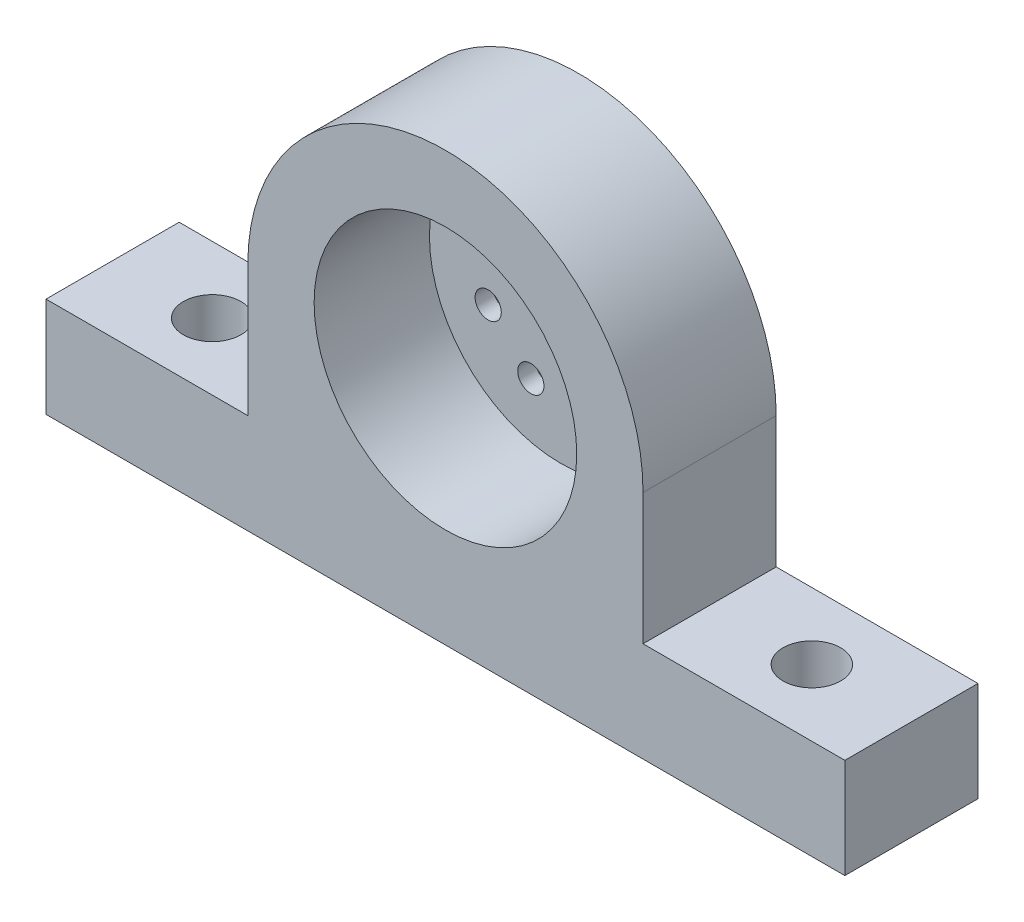
SolidWorks part; units mm, degrees
ref_plane "Front Plane" through (0, 0, 0) normal (0, 0, 1) x (1, 0, 0)
ref_plane "Top Plane" through (0, 0, 0) normal (0, 1, 0) x (1, 0, 0)
ref_plane "Right Plane" through (0, 0, 0) normal (1, 0, 0) x (0, 0, -1)
sketch "Sketch1" plane through (0, 0, 0) normal (0, 0, 1) x (1, 0, 0)
  line L0 (0, 0) -> (0, -56.069) construction
  line L1 (-76.2, -44.05) -> (76.2, -44.05)
  line L2 (-76.2, -44.05) -> (-76.2, -25)
  line L3 (-76.2, -25) -> (76.2, -25)
  line L4 (76.2, -44.05) -> (76.2, -25)
  line L5 (-76.2, -44.05) -> (76.2, -25) construction
  line L6 (-76.2, -25) -> (76.2, -44.05) construction
  line L8 (-37.7, -25) -> (37.7, -25)
  line L9 (-37.7, -25) -> (-37.7, 0)
  line L10 (-37.7, 0) -> (37.7, 0)
  line L11 (37.7, -25) -> (37.7, 0)
  line L12 (-37.7, -25) -> (37.7, 0) construction
  line L13 (-37.7, 0) -> (37.7, -25) construction
  circle A0 centre (0, 0) radius 25
  circle A1 centre (0, 0) radius 20.5
  circle A2 centre (0, 0) radius 12.5
  circle A3 centre (-14.5296, 0.4704) radius 2.5
  circle A4 centre (-10.1362, 11.077) radius 2.5
  circle A5 centre (0.4704, 15.4704) radius 2.5
  circle A6 centre (11.077, 11.077) radius 2.5
  circle A7 centre (15.4704, 0.4704) radius 2.5
  circle A8 centre (11.077, -10.1362) radius 2.5
  circle A9 centre (0, -14.5296) radius 2.5
  circle A10 centre (-10.1362, -10.1362) radius 2.5
  circle A11 centre (0, 0) radius 4
  circle A12 centre (0, 0) radius 10
  arc A13 (-37.7, 0) -> (37.7, 0) centre (0, 0) cw
  point P22 (0, -34.525)
  point P27 (0, -12.5)
  point P34 (-25, 0)
  point P35 (25, 0)
  dimension "D3" = 0
  dimension "D1" = 152.4
  dimension "D2" = 19.05
  dimension "D4" = 0
  dimension "D5" = 12.7
extrude "Boss-Extrude1" add sketch "Sketch1" along normal blind 25.4 contours L1 L4 L3 L8 L2 | A0 L10 L9 L3 | A13 L10 A0 | A1 L10 A0 | A1 L10 A0 | A10 A2 A3 L10 A1 A7 A9 A8 | A7 L10 A1 A3 A2 A6 A5 A4 | A12 L10 A2 A3 | A12 L10 A3 A2 A10 A9 | L10 A12 A11 | L10 A12 A11 | A0 L8 L11 L10
sketch "Sketch3" plane through (0, 0, 25.4) normal (0, 0, 1) x (1, 0, 0)
  circle A0 centre (0, 0) radius 25.05
  dimension "D1" = 50.1
extrude "Cut-Extrude1" cut sketch "Sketch3" against normal blind 22
sketch "Sketch4" plane through (0, -25, 0) normal (0, 1, 0) x (1, 0, 0)
  line L0 (-76.2, -12.7) -> (76.2, -12.7) construction
  line L1 (-76.2, -25.4) -> (-76.2, 0) construction
  line L2 (76.2, -25.4) -> (76.2, 0) construction
  line L3 (57.2, -25.4) -> (57.2, 0) construction
  line L6 (-57.2, -25.4) -> (-57.2, 0) construction
  point P18 (-57.2, -12.7)
  point P19 (57.2, -12.7)
  dimension "D1" = 19
  dimension "D2" = 19
hole_wizard "M10 Clearance Hole1" positions "Sketch6" profile "Sketch7" hole size "M10" standard "ANSI Metric" end condition through all
sketch "Sketch6" plane through (0, -25, 0) normal (0, 1, 0) x (1, 0, 0)
  point P0 (-57.2, -12.7)
  point P3 (57.2, -12.7)
sketch "Sketch7" plane through (-57.2, -25, 12.7) normal (1, 0, 0) x (0, 0, 1)
  line L0 (0, 0) -> (0, 19.05)
  line L1 (0, 19.05) -> (5.5, 19.05)
  line L2 (5.5, 19.05) -> (5.5, 0)
  line L5 (5.5, 0) -> (0, 0)
  line L11 (0, -6.35) -> (0, 107.95) construction
  dimension "Thru Hole Dia." = 11
  dimension "Thru Hole Depth" = 19.05
sketch "Sketch11" plane through (0, 0, 0) normal (0, 0, -1) x (-1, 0, 0)
  line L0 (0, 15) -> (0, 0) construction
  line L1 (0, 0) -> (-5.7053, 13.8726) construction
  circle A0 centre (-15, 0) radius 2.5
  circle A1 centre (-10.6066, -10.6066) radius 2.5
  circle A2 centre (0, -15) radius 2.5
  circle A3 centre (10.6066, -10.6066) radius 2.5
  circle A4 centre (15, 0) radius 2.5
  circle A5 centre (10.6066, 10.6066) radius 2.5
  circle A6 centre (0, 15) radius 2.5
  circle A7 centre (-10.6066, 10.6066) radius 2.5
  circle A8 centre (-5.7053, 13.8726) radius 2.5
  circle A9 centre (-13.8437, 5.7751) radius 2.5
  circle A10 centre (-13.8726, -5.7053) radius 2.5
  circle A11 centre (-5.7751, -13.8437) radius 2.5
  circle A12 centre (5.7053, -13.8726) radius 2.5
  circle A13 centre (13.8437, -5.7751) radius 2.5
  circle A14 centre (13.8726, 5.7053) radius 2.5
  circle A15 centre (5.7751, 13.8437) radius 2.5
  point P0 (0, 0)
  dimension "D1" = 22.356
extrude "Cut-Extrude2" cut sketch "Sketch11" against normal blind 10 contours A15 | A8 | A9 | A10 | A11 | A12 | A13 | A14
